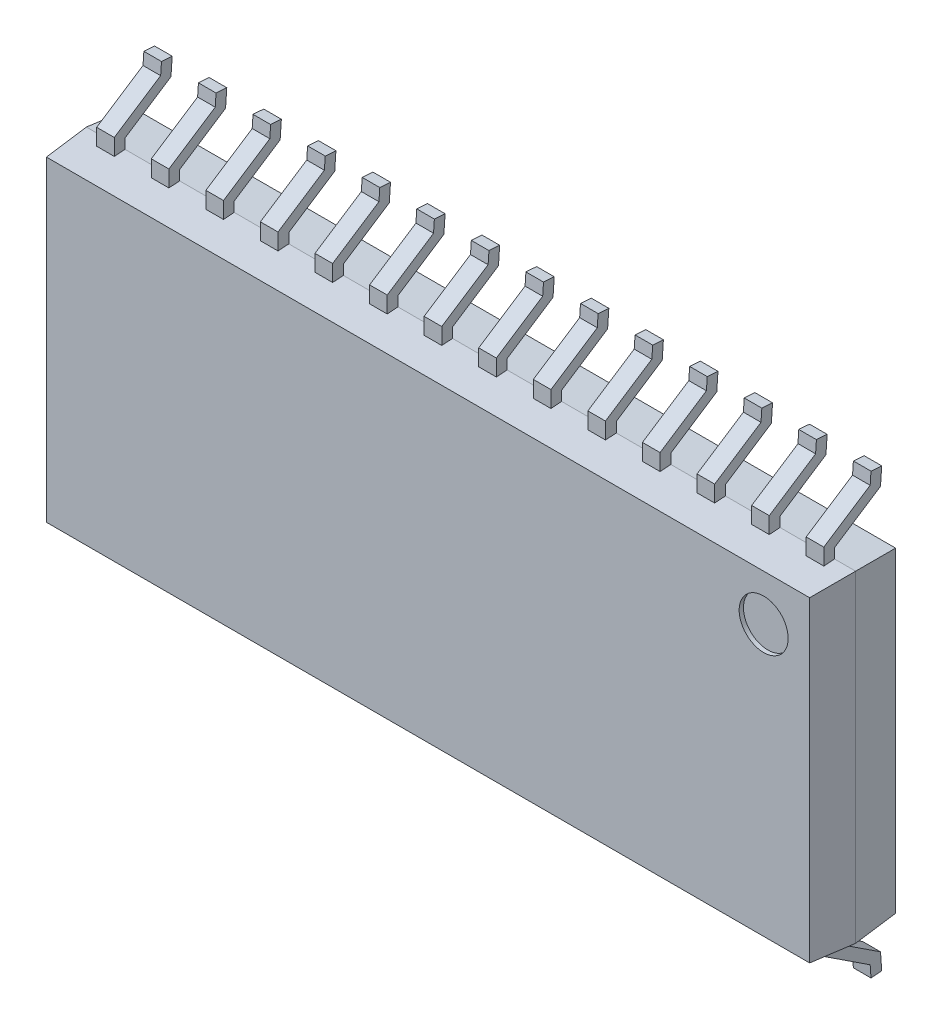
SolidWorks part; units mm, degrees
ref_plane "Front Plane" through (0, 0, 0) normal (0, 0, 1) x (1, 0, 0)
ref_plane "Top Plane" through (0, 0, 0) normal (0, 1, 0) x (1, 0, 0)
ref_plane "Right Plane" through (0, 0, 0) normal (1, 0, 0) x (0, 0, -1)
sketch "Sketch1" plane through (0, 0, 0) normal (0, 0, 1) x (1, 0, 0)
  line L1 (0, 0) -> (17.9, 0)
  line L2 (0, 0) -> (0, 7.5)
  line L3 (0, 7.5) -> (17.9, 7.5)
  line L4 (17.9, 0) -> (17.9, 7.5)
  dimension "D1" = 17.9
  dimension "D2" = 7.5
extrude "Boss-Extrude1" add sketch "Sketch1" along normal blind 1 draft 4
sketch "Sketch2" plane through (0, 0, 0) normal (0, 0, -1) x (-1, 0, 0)
  line L1 (-17.9, 7.5) -> (0, 7.5)
  line L2 (-17.9, 7.5) -> (-17.9, 0)
  line L3 (-17.9, 0) -> (0, 0)
  line L4 (0, 7.5) -> (0, 0)
extrude "Boss-Extrude2" add sketch "Sketch2" along normal blind 1 draft 4 separate body
ref_plane "Plane1" through (0.695, 0, 0) normal (1, 0, 0) x (0, 0, -1)
sketch "Sketch3" plane through (0.695, 0, 0) normal (1, 0, 0) x (0, 0, -1)
  line L0 (0, 0.1503) -> (0, -0.2497)
  line L1 (0, -0.2497) -> (1.0689, -0.9497)
  line L2 (1.0689, -0.9497) -> (1.0969, -1.3497)
  line L3 (1.0689, -1.1) -> (1.0689, -4.5316) construction
  dimension "D2" = 0.4
  dimension "D3" = 4
  dimension "D5" = 0.4
  dimension "D6" = 1.5
extrude "Extrude-Thin3" add sketch "Sketch3" along normal mid plane 0.41 separate body thin
pattern_linear "LPattern1" count 14 spacing 1.27 along (1, 0, 0) of "Extrude-Thin3"
ref_plane "Plane2" through (0, 3.74, 0) normal (0, 1, 0) x (1, 0, 0)
mirror "Mirror3" about plane through (0, 3.74, 0) normal (0, 1, 0) of "Extrude-Thin3", "LPattern1"
sketch "Sketch4" plane through (0, 0, 1) normal (0, 0, 1) x (1, 0, 0)
  line L0 (17.9, 0) -> (17.9, 7.5) construction
  line L1 (17.9, 7.5) -> (17.41, 7.5) construction
  circle A0 centre (16.76, 6.36) radius 0.57
  dimension "D1" = 1.14
  dimension "D2" = 1.14
  dimension "D3" = 1.14
extrude "Cut-Extrude1" cut sketch "Sketch4" against normal blind 0.1
